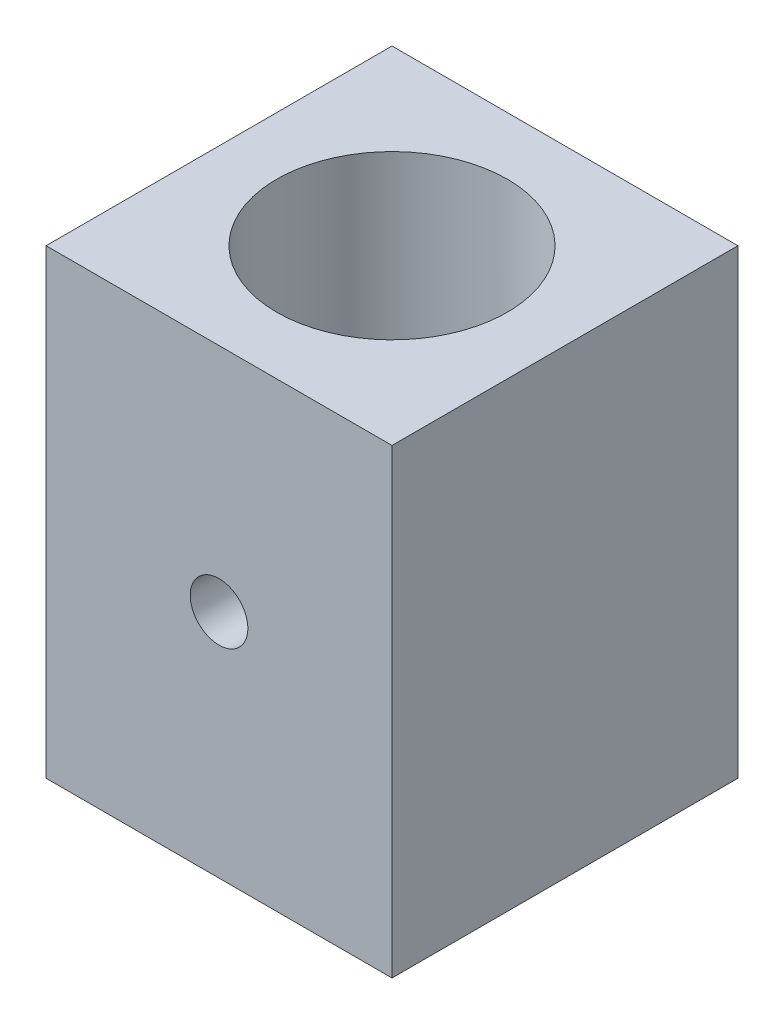
SolidWorks part; units mm, degrees
ref_plane "Front Plane" through (0, 0, 0) normal (0, 0, 1) x (1, 0, 0)
ref_plane "Top Plane" through (0, 0, 0) normal (0, 1, 0) x (1, 0, 0)
ref_plane "Right Plane" through (0, 0, 0) normal (1, 0, 0) x (0, 0, -1)
sketch "Sketch3" plane through (0, 0, 0) normal (0, 1, 0) x (1, 0, 0)
  line L1 (0, 0) -> (76.2, 0)
  line L2 (0, 0) -> (0, 76.2)
  line L3 (0, 76.2) -> (76.2, 76.2)
  line L4 (76.2, 0) -> (76.2, 76.2)
  dimension "D1" = 76.2
  dimension "D2" = 76.2
extrude "Boss-Extrude2" add sketch "Sketch3" along normal blind 101.6
sketch "Sketch4" plane through (0, 0, 0) normal (0, 0, 1) x (1, 0, 0)
  line L0 (0, 101.6) -> (76.2, 101.6) construction
  line L2 (76.2, 101.6) -> (76.2, 0) construction
  circle A0 centre (38.1, 50.8) radius 6.35
  dimension "D1" = 12.7
  dimension "D2" = 50.8
  dimension "D3" = 38.1
extrude "Cut-Extrude2" cut sketch "Sketch4" against normal blind 73.914
sketch "Sketch5" plane through (0, 101.6, 0) normal (0, 1, 0) x (1, 0, 0)
  line L0 (76.2, 76.2) -> (0, 76.2) construction
  line L1 (76.2, 0) -> (76.2, 76.2) construction
  circle A0 centre (38.1, 38.1) radius 25.4
  dimension "D1" = 50.8
  dimension "D2" = 38.1
  dimension "D3" = 38.1
extrude "Cut-Extrude3" cut sketch "Sketch5" against normal blind 113.538
sketch "Sketch7" plane through (0, 0, -76.2) normal (0, 0, -1) x (-1, 0, 0)
  line L0 (-76.2, 101.6) -> (-76.2, 0) construction
  line L1 (-76.2, 0) -> (0, 0) construction
  circle A0 centre (-38.1, 50.8) radius 6.35
  dimension "D1" = 38.1
  dimension "D3" = 12.7
  dimension "D2" = 50.8
extrude "Cut-Extrude4" cut sketch "Sketch7" against normal blind 18.034
